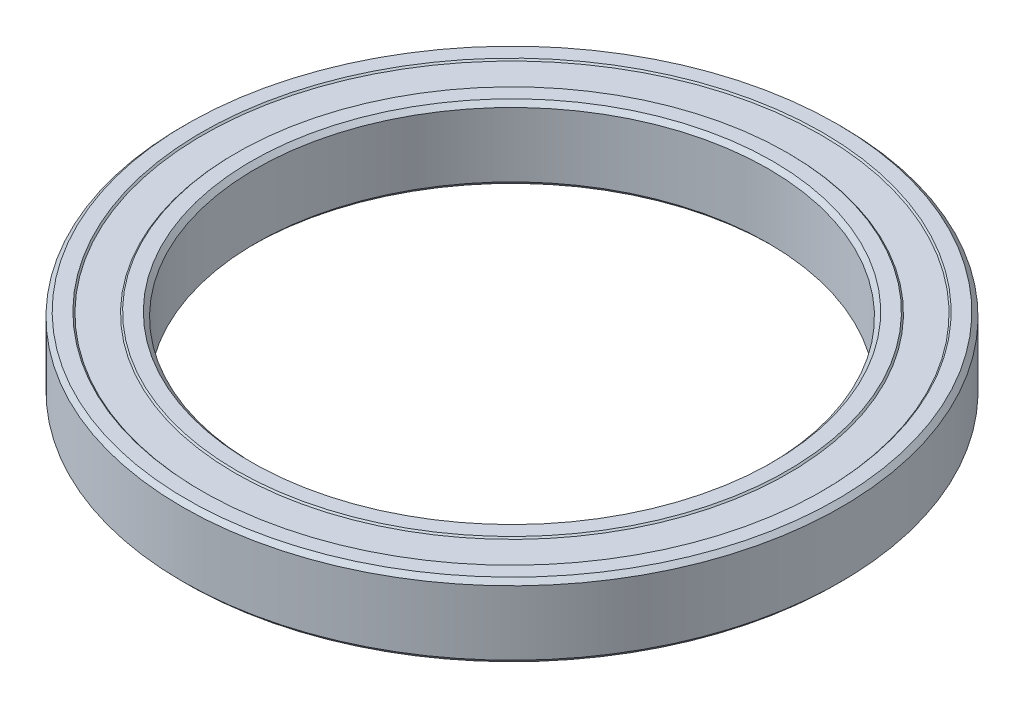
SolidWorks part; units mm, degrees
material "Stainless Steel (ferritic)"
ref_plane "Front Plane" through (0, 0, 0) normal (0, 0, 1) x (1, 0, 0)
ref_plane "Top Plane" through (0, 0, 0) normal (0, 1, 0) x (1, 0, 0)
ref_plane "Right Plane" through (0, 0, 0) normal (1, 0, 0) x (0, 0, -1)
sketch "Sketch1" plane through (0, 0, 0) normal (0, 0, 1) x (1, 0, 0)
  line L0 (0, -1.3494) -> (0, 70.5256) construction
  line L1 (35, 4.4) -> (35, -4.4)
  line L2 (35, -4.4) -> (35.6, -5)
  line L3 (35.6, -5) -> (37.6, -5)
  line L4 (37.6, -5) -> (37.8, -4.8)
  line L5 (37.8, -4.8) -> (42.2, -4.8)
  line L6 (42.2, -4.8) -> (42.4, -5)
  line L7 (42.4, -5) -> (44.4, -5)
  line L8 (44.4, -5) -> (45, -4.4)
  line L9 (45, -4.4) -> (45, 4.4)
  line L10 (45, 4.4) -> (44.4, 5)
  line L11 (44.4, 5) -> (42.4, 5)
  line L12 (42.4, 5) -> (42.2, 4.8)
  line L13 (42.2, 4.8) -> (37.8, 4.8)
  line L14 (37.8, 4.8) -> (37.6, 5)
  line L15 (37.6, 5) -> (35.6, 5)
  line L16 (35.6, 5) -> (35, 4.4)
  line L17 (0, 0) -> (35, 0) construction
  dimension "D1" = 35
  dimension "D2" = 10
  dimension "D3" = 0.6
  dimension "D4" = 0.2
  dimension "D5" = 45
  dimension "D6" = 2
revolve "Revolve1" add sketch "Sketch1" angle 360 about L0
